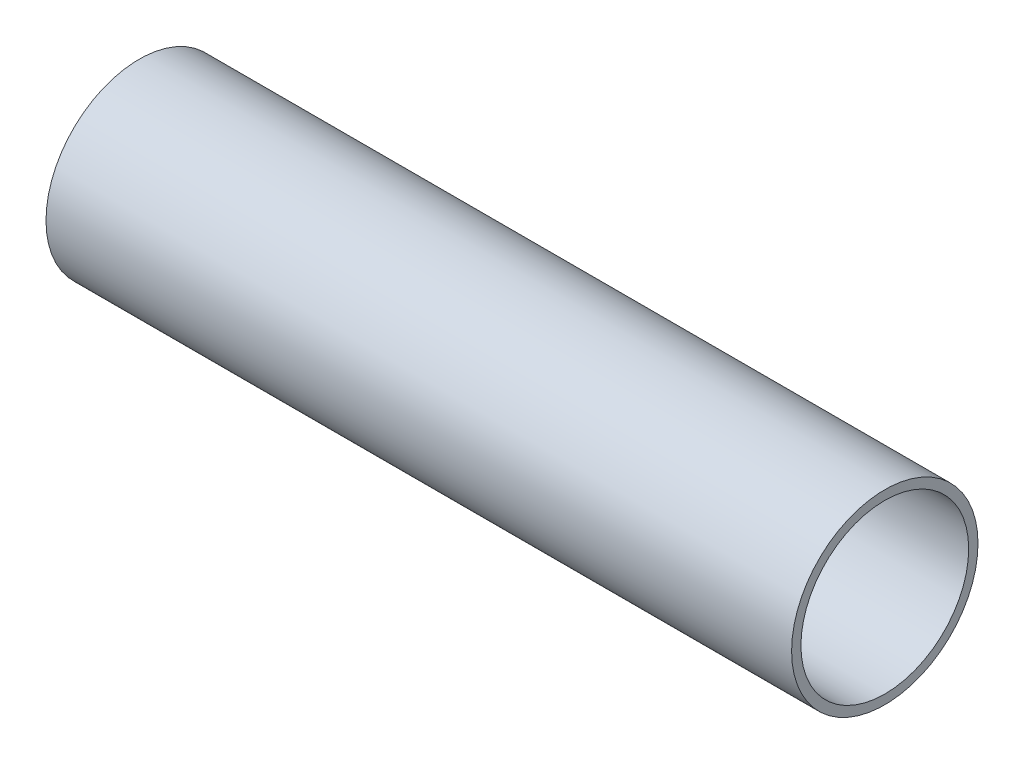
SolidWorks part; units mm, degrees
material "6061-T6 (SS)"
ref_plane "Front Plane" through (0, 0, 0) normal (0, 0, 1) x (1, 0, 0)
ref_plane "Top Plane" through (0, 0, 0) normal (0, 1, 0) x (1, 0, 0)
ref_plane "Right Plane" through (0, 0, 0) normal (1, 0, 0) x (0, 0, -1)
sketch "Sketch1" plane through (0, 0, 0) normal (1, 0, 0) x (0, 0, -1)
  circle A0 centre (0, 0) radius 6.35
  dimension "D1" = 12.7
extrude "Boss-Extrude1" add sketch "Sketch1" along normal blind 50.8
sketch "Sketch2" plane through (50.8, 0, 0) normal (1, 0, 0) x (0, 0, -1)
  circle A0 centre (0, 0) radius 5.715
  dimension "D1" = 11.43
extrude "Cut-Extrude1" cut sketch "Sketch2" against normal through all
